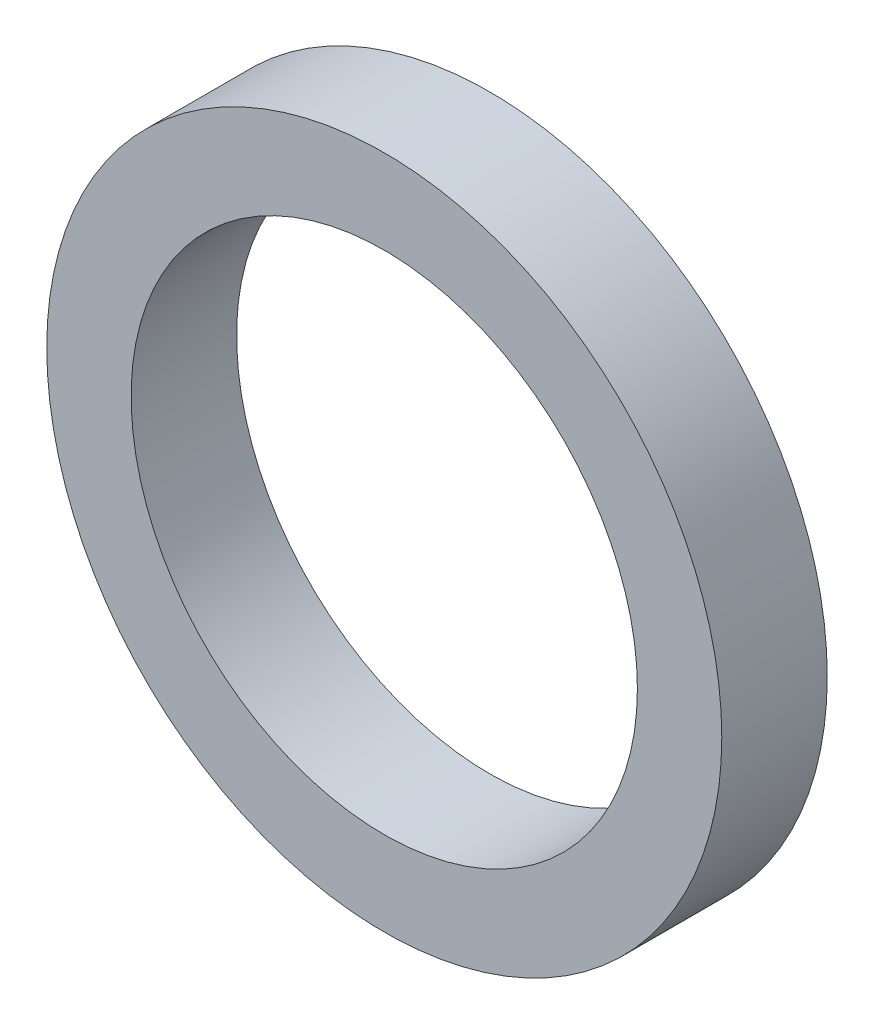
SolidWorks part; units mm, degrees
material "Alloy Steel (SS)"
ref_plane "Front Plane" through (0, 0, 0) normal (0, 0, 1) x (1, 0, 0)
ref_plane "Top Plane" through (0, 0, 0) normal (0, 1, 0) x (1, 0, 0)
ref_plane "Right Plane" through (0, 0, 0) normal (1, 0, 0) x (0, 0, -1)
sketch "Sketch1" plane through (0, 0, 0) normal (0, 0, 1) x (1, 0, 0)
  circle A0 centre (0, 0) radius 6
  circle A1 centre (0, 0) radius 8
  dimension "D1" = 16
  dimension "12" = 12
extrude "Boss-Extrude1" add sketch "Sketch1" along normal blind 2.5
